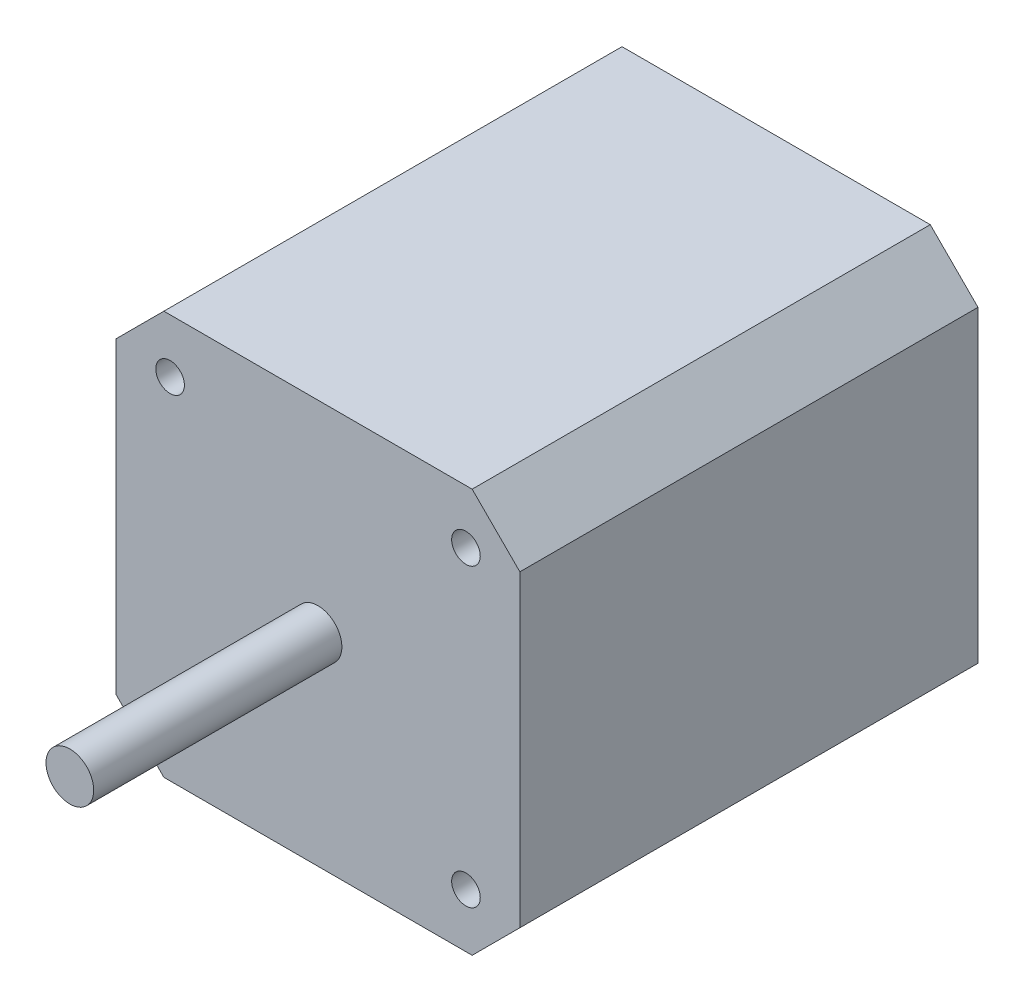
SolidWorks part; units mm, degrees
ref_plane "Piano frontale" through (0, 0, 0) normal (0, 0, 1) x (1, 0, 0)
ref_plane "Piano superiore" through (0, 0, 0) normal (0, 1, 0) x (1, 0, 0)
ref_plane "Piano destro" through (0, 0, 0) normal (1, 0, 0) x (0, 0, -1)
sketch "Schizzo1" plane through (0, 0, 0) normal (0, 0, 1) x (1, 0, 0)
  line L1 (-21.15, -21.15) -> (21.15, -21.15)
  line L2 (-21.15, -21.15) -> (-21.15, 21.15)
  line L3 (-21.15, 21.15) -> (21.15, 21.15)
  line L4 (21.15, -21.15) -> (21.15, 21.15)
  line L5 (-21.15, -21.15) -> (21.15, 21.15) construction
  line L6 (-21.15, 21.15) -> (21.15, -21.15) construction
  point P0 (0, 0)
  dimension "D1" = 42.3
  dimension "D2" = 42.3
extrude "Estrusione-Estrusione1" add sketch "Schizzo1" along normal blind 48
chamfer "Smusso1" distance 5 angle 45 4 edges at (21.15, -21.15, 24) (-21.15, -21.15, 24) (-21.15, 21.15, 24) (21.15, 21.15, 24)
sketch "Schizzo2" plane through (0, 0, 48) normal (0, 0, 1) x (1, 0, 0)
  circle A0 centre (0, 0) radius 2.5
  dimension "D1" = 5
extrude "Estrusione-Estrusione2" add sketch "Schizzo2" along normal blind 26
sketch "Schizzo3" plane through (0, 0, 0) normal (0, 0, -1) x (-1, 0, 0)
  line L0 (16.15, -21.15) -> (-16.15, -21.15) construction
  line L2 (-1.15, -21.15) -> (-1.15, -36.15)
  line L3 (-1.15, -36.15) -> (1.15, -36.15)
  line L4 (1.15, -21.15) -> (1.15, -36.15)
  line L5 (0, -21.15) -> (1.15, -36.15) construction
  line L6 (-1.15, -36.15) -> (0, -21.15) construction
  line L7 (-1.15, -21.15) -> (1.15, -21.15)
  point P0 (0, -21.15)
  point P9 (0, -36.15)
  dimension "D1" = 15
  dimension "D2" = 15
  dimension "D3" = 15
  dimension "D4" = 15
extrude "Estrusione-Estrusione3" add sketch "Schizzo3" against normal blind 5
sketch "Schizzo4" plane through (0, 0, 48) normal (0, 0, 1) x (1, 0, 0)
  line L1 (-15.5, -15.5) -> (15.5, -15.5) construction
  line L2 (-15.5, -15.5) -> (-15.5, 15.5) construction
  line L3 (-15.5, 15.5) -> (15.5, 15.5) construction
  line L4 (15.5, -15.5) -> (15.5, 15.5) construction
  line L5 (-15.5, -15.5) -> (15.5, 15.5) construction
  line L6 (-15.5, 15.5) -> (15.5, -15.5) construction
  circle A0 centre (-15.5, 15.5) radius 1.5
  circle A1 centre (-15.5, -15.5) radius 1.5
  circle A2 centre (15.5, -15.5) radius 1.5
  circle A3 centre (15.5, 15.5) radius 1.5
  point P0 (0, 0)
  dimension "D3" = 3
  dimension "D1" = 31
  dimension "D2" = 31
extrude "Taglio-Estrusione1" cut sketch "Schizzo4" against normal blind 5
